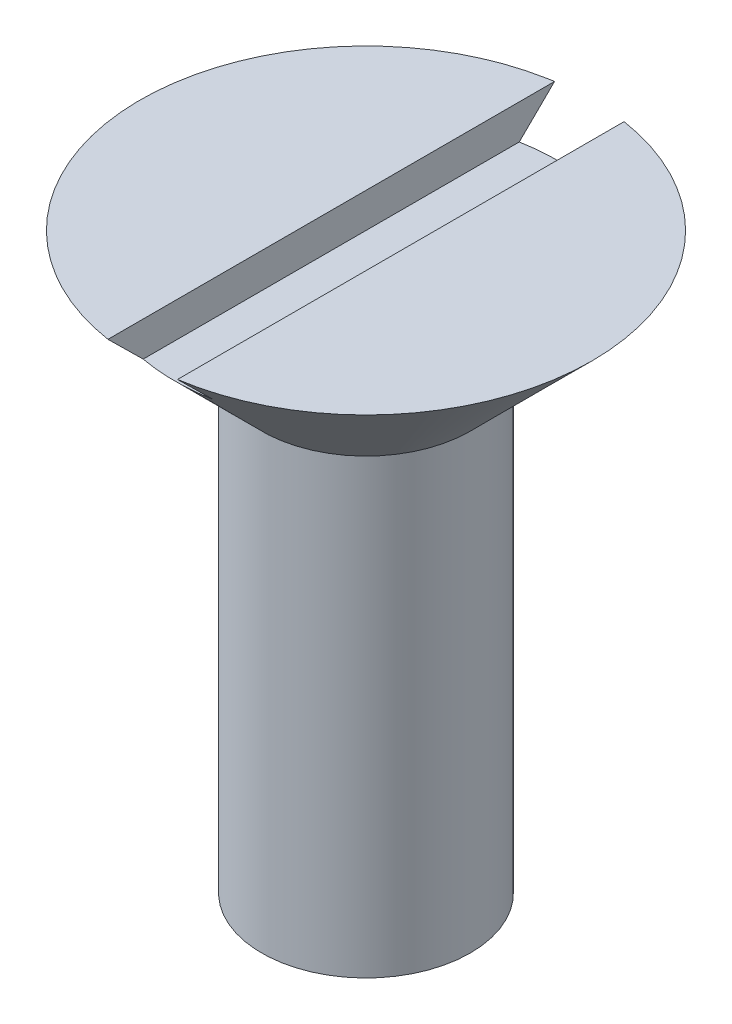
SolidWorks part; units mm, degrees
ref_plane "Front Plane" through (0, 0, 0) normal (0, 0, 1) x (1, 0, 0)
ref_plane "Top Plane" through (0, 0, 0) normal (0, 1, 0) x (1, 0, 0)
ref_plane "Right Plane" through (0, 0, 0) normal (1, 0, 0) x (0, 0, -1)
sketch "Sketch2" plane through (0, 0, 0) normal (0, 0, 1) x (1, 0, 0)
  line L0 (0, 0) -> (0, 18.2321)
  line L1 (0, 18.2321) -> (6.5, 18.2321)
  line L2 (6.5, 18.2321) -> (3, 14.7321)
  line L3 (3, 14.7321) -> (3, 1.7321)
  line L4 (3, 1.7321) -> (0, 0)
  dimension "D1" = 60
  dimension "D2" = 3
  dimension "D3" = 6.5
  dimension "D4" = 135
  dimension "D5" = 13
revolve "Revolve1" add sketch "Sketch2" angle 360 about L0
sketch "Sketch3" plane through (0, 18.2321, 0) normal (0, 1, 0) x (1, 0, 0)
  line L1 (1, 7.5) -> (-1, 7.5)
  line L2 (1, 7.5) -> (1, -7.5)
  line L3 (1, -7.5) -> (-1, -7.5)
  line L4 (-1, 7.5) -> (-1, -7.5)
  line L5 (1, 7.5) -> (-1, -7.5) construction
  line L6 (1, -7.5) -> (-1, 7.5) construction
  point P0 (0, 0)
  dimension "D1" = 2
  dimension "D2" = 15
extrude "Cut-Extrude1" cut sketch "Sketch3" against normal blind 1
